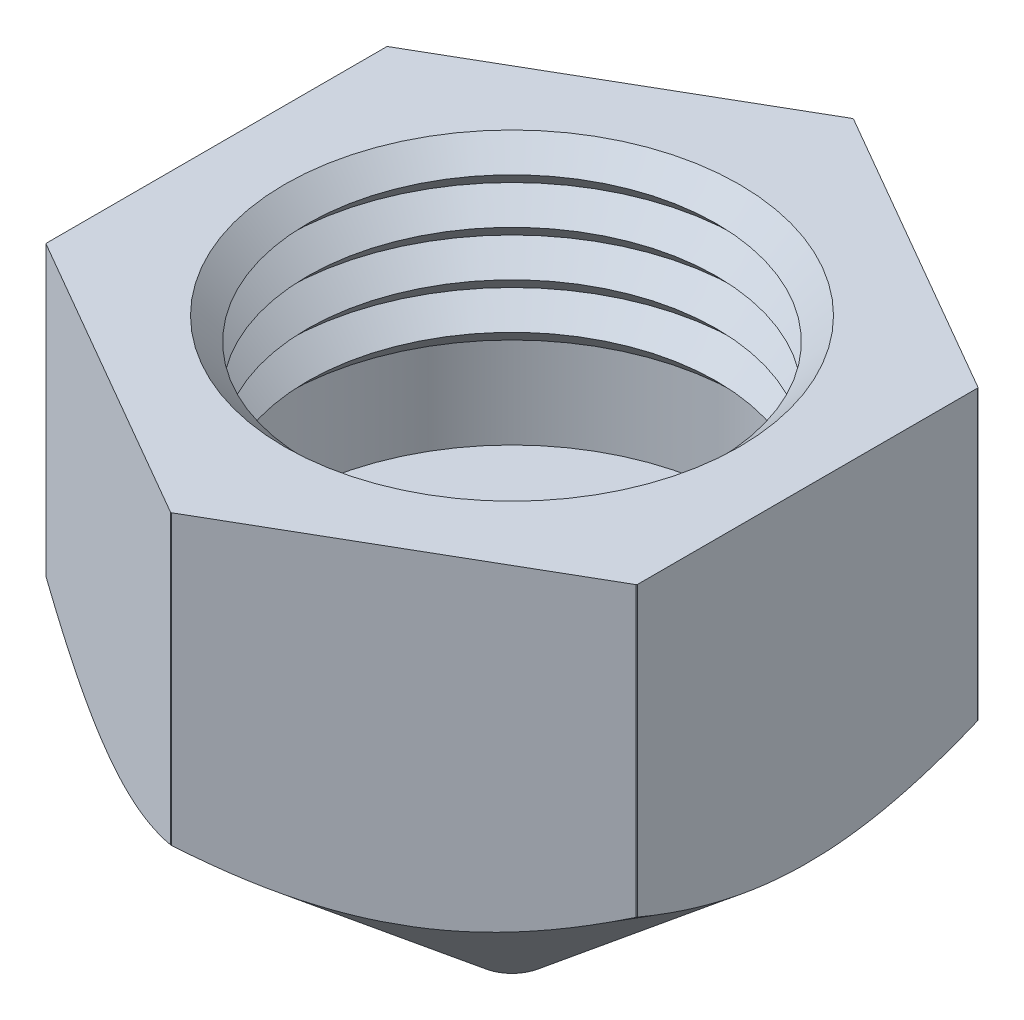
SolidWorks part; units mm, degrees
material "6061-T6 (SS)"
ref_plane "Front Plane" through (0, 0, 0) normal (0, 0, 1) x (1, 0, 0)
ref_plane "Top Plane" through (0, 0, 0) normal (0, 1, 0) x (1, 0, 0)
ref_plane "Right Plane" through (0, 0, 0) normal (1, 0, 0) x (0, 0, -1)
sketch "Sketch1" plane through (0, 0, 0) normal (0, 0, 1) x (1, 0, 0)
  line L0 (0, 0) -> (0, -21.5428) construction
  line L1 (5, 0) -> (5, -5.969) construction
  line L2 (0.25, -12) -> (0.75, -12)
  line L3 (1.5875, -6.5) -> (1.5875, -9.906)
  line L4 (1.5875, -9.906) -> (0.25, -11.5)
  line L5 (0.25, -11.5) -> (0.25, -12)
  line L6 (2.0875, -6) -> (1.5875, -6.5)
  line L7 (4.5, -1.5) -> (5, -1)
  line L8 (5, -6) -> (2.0875, -6)
  line L9 (0.75, -12) -> (7.5, -6.3361)
  line L10 (5, -4) -> (5, -6)
  line L11 (5, -1) -> (4.5, -0.5)
  line L12 (4.5, -0.5) -> (5, 0)
  line L14 (7.5, -6.3361) -> (7.5, 0)
  line L15 (7.5, 0) -> (5, 0)
  line L29 (4.5, -9.525) -> (4.5, 0) construction
  line L32 (5, -4) -> (4.5, -3.5)
  line L33 (4.5, -3.5) -> (5, -3)
  line L34 (5, -3) -> (4.5, -2.5)
  line L35 (4.5, -2.5) -> (5, -2)
  line L36 (5, -2) -> (4.5, -1.5)
  point P6 (1.5875, -6)
  dimension "D1" = 15
  dimension "D2" = 3.175
  dimension "D3" = 5
  dimension "D4" = 4.5
  dimension "D5" = 50
  dimension "D6" = 12
  dimension "D7" = 6
  dimension "D8" = 2
  dimension "D9" = 1.5
  dimension "D10" = 0.5
  dimension "D11" = 0.5
  dimension "D12" = 1
  dimension "D14" = 40
  dimension "D15" = 0.5
revolve "Revolve1" add sketch "Sketch1" angle 360 about L0
sketch "Sketch2" plane through (0, 0, 0) normal (0, 1, 0) x (1, 0, 0)
  line L1 (0, 7.5056) -> (-6.5, 3.7528)
  line L2 (-6.5, 3.7528) -> (-6.5, -3.7528)
  line L3 (-6.5, -3.7528) -> (0, -7.5056)
  line L4 (0, -7.5056) -> (6.5, -3.7528)
  line L5 (6.5, -3.7528) -> (6.5, 3.7528)
  line L6 (6.5, 3.7528) -> (0, 7.5056)
  circle A0 centre (0, 0) radius 6.5 construction
  dimension "D1" = 13
extrude "Cut-Extrude1" cut sketch "Sketch2" against normal through all flip side to cut
